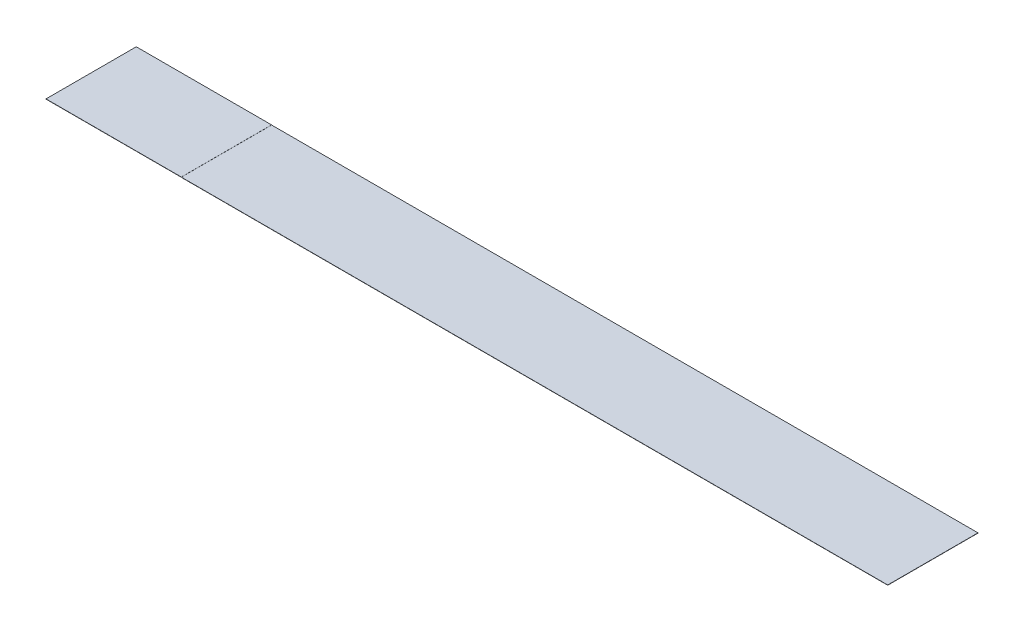
SolidWorks part; units mm, degrees
material "Generic Carbon Fiber"
ref_plane "Front Plane" through (0, 0, 0) normal (0, 0, 1) x (1, 0, 0)
ref_plane "Top Plane" through (0, 0, 0) normal (0, 1, 0) x (1, 0, 0)
ref_plane "Right Plane" through (0, 0, 0) normal (1, 0, 0) x (0, 0, -1)
sketch "Sketch1" plane through (0, 0, 0) normal (0, 1, 0) x (1, 0, 0)
  line L1 (-264.4, 30.5) -> (264.4, 30.5)
  line L2 (-264.4, 30.5) -> (-264.4, -30.5)
  line L3 (-264.4, -30.5) -> (264.4, -30.5)
  line L4 (264.4, 30.5) -> (264.4, -30.5)
  line L5 (-264.4, 30.5) -> (264.4, -30.5) construction
  line L6 (-264.4, -30.5) -> (264.4, 30.5) construction
  point P0 (0, 0)
  dimension "D1" = 528.8
  dimension "D2" = 61
extrude "Extrude1" add sketch "Sketch1" along normal blind 0.15
sketch "Sketch3" plane through (0, 0.15, 0) normal (0, 1, 0) x (1, 0, 0)
  line L0 (-264.4, -30.5) -> (264.4, -30.5) construction
  line L1 (-264.4, 30.5) -> (-284.4, 30.5)
  line L2 (-264.4, 30.5) -> (-264.4, -30.5)
  line L3 (-264.4, -30.5) -> (-284.4, -30.5)
  line L4 (-284.4, 30.5) -> (-284.4, -30.5)
  line L6 (264.4, 30.5) -> (284.4, 30.5)
  line L7 (264.4, 30.5) -> (264.4, -30.5)
  line L8 (264.4, -30.5) -> (284.4, -30.5)
  line L9 (284.4, 30.5) -> (284.4, -30.5)
  dimension "D1" = 20
  dimension "D2" = 20
extrude "Boss-Extrude2" add sketch "Sketch3" against normal up to surface (0.15 mm away) up to face at (0, 0, 0)
sketch "Sketch5" plane through (0, 0, 30.5) normal (0, 0, 1) x (1, 0, 0)
  line L1 (-284.4, 0.15) -> (-192.95, 0.15)
  line L2 (-284.4, 0.15) -> (-284.4, 0.2186)
  line L3 (-284.4, 0.2186) -> (-192.95, 0.2186)
  line L4 (-192.95, 0.15) -> (-192.95, 0.2186)
  dimension "D1" = 91.45
  dimension "D2" = 0.0686
extrude "Boss-Extrude4" add sketch "Sketch5" against normal up to surface (61 mm away) up to face at (0, 0.075, -30.5)
sketch "Sketch6" plane through (0, 0, 30.5) normal (0, 0, 1) x (1, 0, 0)
  line L1 (-284.4, 0) -> (-192.95, 0)
  line L2 (-284.4, 0) -> (-284.4, 0.0686)
  line L3 (-284.4, 0.0686) -> (-192.95, 0.0686)
  line L4 (-192.95, 0) -> (-192.95, 0.0686)
  dimension "D1" = 91.45
  dimension "D2" = 0.0686
extrude "Cut-Extrude1" cut sketch "Sketch6" against normal through all
